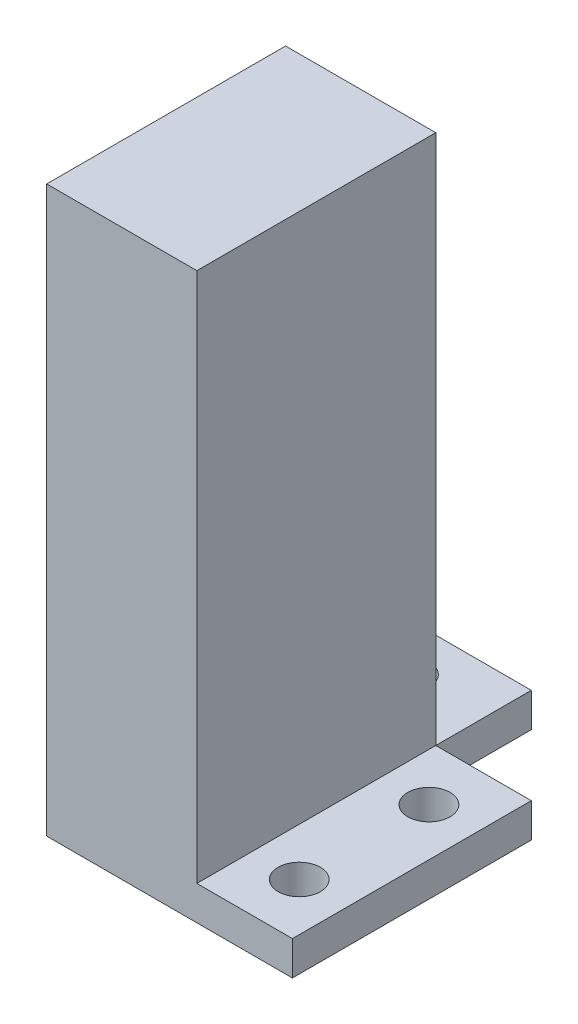
SolidWorks part; units mm, degrees
ref_plane "Front Plane" through (0, 0, 0) normal (0, 0, 1) x (1, 0, 0)
ref_plane "Top Plane" through (0, 0, 0) normal (0, 1, 0) x (1, 0, 0)
ref_plane "Right Plane" through (0, 0, 0) normal (1, 0, 0) x (0, 0, -1)
sketch "Sketch1" plane through (0, 0, 0) normal (0, 0, 1) x (1, 0, 0)
  line L0 (-11, 49.2197) -> (-11, -33.5303)
  line L2 (11, 49.2197) -> (11, -33.5303)
  line L3 (11, 49.2197) -> (-11, 49.2197)
  line L5 (-11, -33.5303) -> (11, -33.5303)
  circle A0 centre (0, 35.7197) radius 3.1
  circle A1 centre (0, 7.7197) radius 3.1
  dimension "D1" = 13.5
  dimension "D2" = 28
  dimension "D3" = 82.75
extrude "Boss-Extrude1" add sketch "Sketch1" along normal blind 30
sketch "Sketch2" plane through (0, 0, 30) normal (0, 0, 1) x (1, 0, 0)
  line L0 (-11, -33.5303) -> (11, -33.5303) construction
  line L2 (11, 49.2197) -> (-11, 49.2197) construction
  line L4 (-11, -33.5303) -> (11, -33.5303)
  line L5 (11, -33.5303) -> (11, 49.2197)
  line L6 (11, 49.2197) -> (-11, 49.2197)
  line L7 (-11, 49.2197) -> (-11, -33.5303)
extrude "Boss-Extrude2" add sketch "Sketch2" along normal blind 5
sketch "Sketch3" plane through (0, -33.5303, 0) normal (0, -1, 0) x (1, 0, 0)
  line L1 (-11, 0) -> (11, 0)
  line L2 (-11, 0) -> (-11, -14)
  line L3 (-11, -14) -> (11, -14)
  line L4 (11, 0) -> (11, -14)
  line L5 (11, 0) -> (25, 0)
  line L6 (11, 0) -> (11, 35)
  line L7 (11, 35) -> (25, 35)
  line L8 (25, 0) -> (25, 35)
  circle A0 centre (18, 8) radius 3.1
  circle A1 centre (18, 27) radius 3.1
  circle A2 centre (0, -7) radius 3.1
  line M3 (-11, 0) -> (11, 0)
  line M4 (11, 0) -> (11, 35)
  dimension "D3" = 6.2
  dimension "D4" = 6.2
  dimension "D5" = 6.2
  dimension "D7" = 8
  dimension "D8" = 11
  dimension "D1" = 14
  dimension "D2" = 14
  dimension "D6" = 8
extrude "Boss-Extrude3" add sketch "Sketch3" against normal blind 5 contours L4 L2 L3 A2 M3 | L5 L8 L7 A1 A0 M4
sketch "Sketch4" plane through (-11, 0, 0) normal (-1, 0, 0) x (0, 0, 1)
  line L6 (0, 49.2197) -> (0, -28.5303)
  line L7 (0, -28.5303) -> (-14, -28.5303)
  line L8 (-14, -28.5303) -> (-14, -33.5303)
  line L9 (-14, -33.5303) -> (35, -33.5303)
  line L10 (35, -33.5303) -> (35, 49.2197)
  line L11 (35, 49.2197) -> (0, 49.2197)
  line L12 (0, 49.2197) -> (0, -28.5303)
  line L13 (0, -28.5303) -> (-14, -28.5303)
  line L14 (-14, -28.5303) -> (-14, -33.5303)
  line L15 (-14, -33.5303) -> (35, -33.5303)
  line L16 (35, -33.5303) -> (35, 49.2197)
  line L17 (35, 49.2197) -> (0, 49.2197)
  dimension "D1" = 0
extrude "Boss-Extrude4" [suppressed] add sketch "Sketch4" along normal blind 2.5
